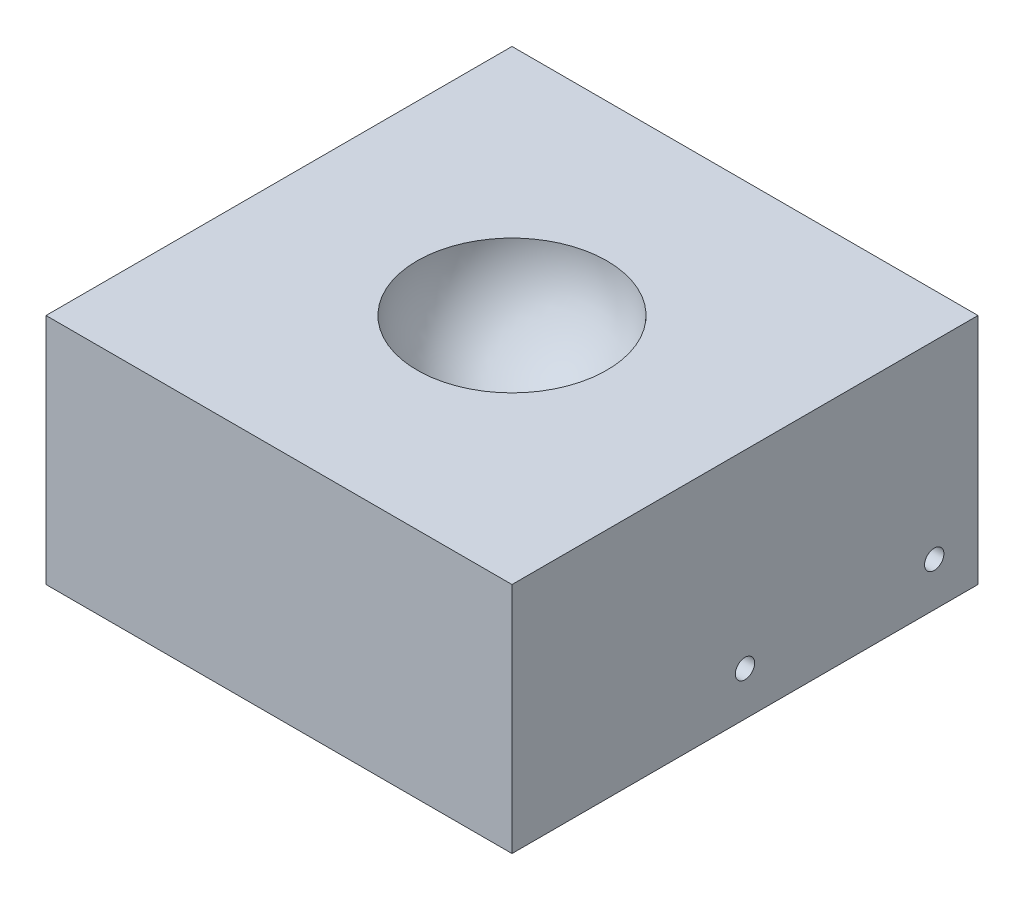
SolidWorks part; units mm, degrees
material "Refractory Clay"
ref_plane "Front Plane" through (0, 0, 0) normal (0, 0, 1) x (1, 0, 0)
ref_plane "Top Plane" through (0, 0, 0) normal (0, 1, 0) x (1, 0, 0)
ref_plane "Right Plane" through (0, 0, 0) normal (1, 0, 0) x (0, 0, -1)
sketch "Sketch1" plane through (0, 0, 0) normal (0, 1, 0) x (1, 0, 0)
  line L1 (-86, -86) -> (86, -86)
  line L2 (-86, -86) -> (-86, 86)
  line L3 (-86, 86) -> (86, 86)
  line L4 (86, -86) -> (86, 86)
  line L5 (-86, -86) -> (86, 86) construction
  line L6 (-86, 86) -> (86, -86) construction
  point P0 (0, 0)
  dimension "D1" = 172
  dimension "D2" = 172
extrude "Boss-Extrude1" add sketch "Sketch1" against normal blind 86
sketch "Sketch2" plane through (0, 0, 0) normal (0, 0, 1) x (1, 0, 0)
  line L0 (-86, 0) -> (86, 0) construction
  line L1 (0, -35) -> (0, 35) construction
  line L2 (0, -35) -> (0, 0)
  line L3 (0, 0) -> (35, 0)
  arc A0 (35, 0) -> (0, -35) centre (0, 0) cw
  dimension "D1" = 35
revolve "Cut-Revolve1" cut sketch "Sketch2" angle 360 about L1
extrude "Cut-Extrude1" cut sketch "Sketch3" against normal through all both and the other way through all
sketch "Sketch3" plane through (0, 0, 0) normal (1, 0, 0) x (0, 0, -1)
  line L0 (0, -69.85) -> (0, 69.85) construction
  line L1 (0, 69.85) -> (-69.85, 69.85) construction
  line L2 (69.85, -69.85) -> (0, -69.85) construction
  circle A0 centre (0, -69.85) radius 3.5687
  circle A1 centre (-69.85, 69.85) radius 3.5687
  circle A2 centre (69.85, -69.85) radius 3.5687
  circle A3 centre (0, 69.85) radius 3.5687
